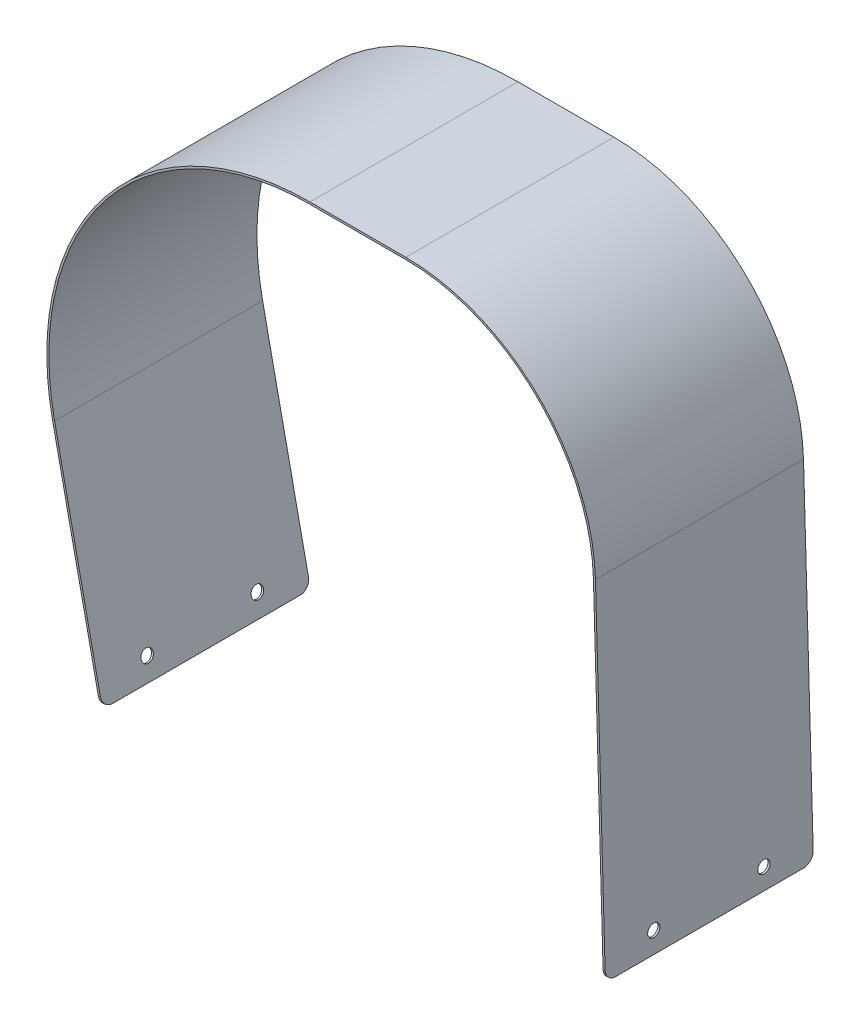
SolidWorks part; units mm, degrees
material "6061-T6 (SS)"
ref_plane "Płaszczyzna przednia" through (0, 0, 0) normal (0, 0, 1) x (1, 0, 0)
ref_plane "Płaszczyzna górna" through (0, 0, 0) normal (0, 1, 0) x (1, 0, 0)
ref_plane "Płaszczyzna prawa" through (0, 0, 0) normal (1, 0, 0) x (0, 0, -1)
sketch "Szkic1" plane through (0, 0, 0) normal (0, 0, 1) x (1, 0, 0)
  line L1 (37.1971, 130) -> (-9.8029, 130)
  line L4 (134.0439, -128) -> (129.1586, 40.6637)
  line L5 (-135.0151, -24.5687) -> (-111.5228, -135.2823)
  arc A3 (-9.8029, 130) -> (-135.0151, -24.5687) centre (-9.8029, 2) ccw
  arc A7 (37.1971, 130) -> (129.1586, 40.6637) centre (37.1971, 38) cw
  dimension "D1" = 129.1586
  dimension "D2" = 92
  dimension "D3" = 128
  dimension "D5" = 128
  dimension "D4" = 135.2823
  dimension "D7" = 9.8029
  dimension "D6" = 47
  dimension "D8" = 130
  dimension "D9" = 135.0151
extrude "Wyciągnięcie-cienka ścianka1" add sketch "Szkic1" along normal blind 102 thin
hole_wizard "Otwór1" positions "Szkic2" profile "Szkic3" legacy end condition up to next
sketch "Szkic2" plane through (131.2267, 3.801, 0) normal (0.9996, 0.029, 0) x (0, 0, -1)
  line L0 (-102, -131.8273) -> (-102, 36.9071) construction
  line L1 (-102, -131.8273) -> (0, -131.8273) construction
  point P0 (-78, -121.8273)
  dimension "D1" = 24
  dimension "D2" = 10
sketch "Szkic3" plane through (134.754, -117.9752, 78) normal (0, 0, 1) x (-0.029, 0.9996, 0)
  line L0 (0, 0) -> (0, 1)
  line L1 (0, 1) -> (3, 1)
  line L2 (3, 1) -> (3, 0)
  line L3 (3, 0) -> (0, 0)
  line L4 (0, 110) -> (0, -10) construction
  dimension "Średnica" = 6
  dimension "Głębokość" = 1
hole_wizard "Otwór2" positions "Szkic4" profile "Szkic5" legacy end condition up to next
sketch "Szkic4" plane through (131.2267, 3.801, 0) normal (0.9996, 0.029, 0) x (0, 0, -1)
  line L0 (0, -131.8273) -> (0, 36.9071) construction
  line L1 (-102, -131.8273) -> (0, -131.8273) construction
  point P0 (-24, -121.8273)
  dimension "D1" = 24
  dimension "D2" = 10
sketch "Szkic5" plane through (134.754, -117.9752, 24) normal (0, 0, 1) x (-0.029, 0.9996, 0)
  line L0 (0, 0) -> (0, 1)
  line L1 (0, 1) -> (3, 1)
  line L2 (3, 1) -> (3, 0)
  line L3 (3, 0) -> (0, 0)
  line L4 (0, 110) -> (0, -10) construction
  dimension "Średnica" = 6
  dimension "Głębokość" = 1
fillet "Zaokrąglenie1" radius 5 4 edges at (134.5437, -127.9855, 102) (134.5437, -127.9855, 0) (-112.0119, -135.3861, 0) (-112.0119, -135.3861, 102)
hole_wizard "Otwór3" positions "Szkic6" profile "Szkic7" legacy end condition up to next
sketch "Szkic6" plane through (-135.1649, -28.6806, 0) normal (-0.9782, -0.2076, 0) x (0, 0, 1)
  line L0 (97, -109.1873) -> (5, -109.1873) construction
  line L1 (0, 3.9912) -> (0, -104.1873) construction
  point P0 (24, -99.1873)
  dimension "10" = 10
  dimension "D2" = 24
sketch "Szkic7" plane through (-114.5767, -125.7077, 24) normal (0, 0, 1) x (0.2076, -0.9782, 0)
  line L0 (0, 0) -> (0, 1)
  line L1 (0, 1) -> (3, 1)
  line L2 (3, 1) -> (3, 0)
  line L3 (3, 0) -> (0, 0)
  line L4 (0, 110) -> (0, -10) construction
  dimension "Średnica" = 6
  dimension "Głębokość" = 1
hole_wizard "Otwór4" positions "Szkic11" profile "Szkic10" legacy end condition up to next
sketch "Szkic11" plane through (-135.1649, -28.6806, 0) normal (-0.9782, -0.2076, 0) x (0, 0, 1)
  line L0 (97, -109.1873) -> (5, -109.1873) construction
  line L3 (102, 3.9912) -> (102, -104.1873) construction
  point P0 (78, -99.1873)
  dimension "D1" = 10
  dimension "D2" = 24
sketch "Szkic10" plane through (-114.5767, -125.7077, 78) normal (0, 0, 1) x (0.2076, -0.9782, 0)
  line L0 (0, 0) -> (0, 1)
  line L1 (0, 1) -> (3, 1)
  line L2 (3, 1) -> (3, 0)
  line L3 (3, 0) -> (0, 0)
  line L4 (0, 110) -> (0, -10) construction
  dimension "Średnica" = 6
  dimension "Głębokość" = 1
